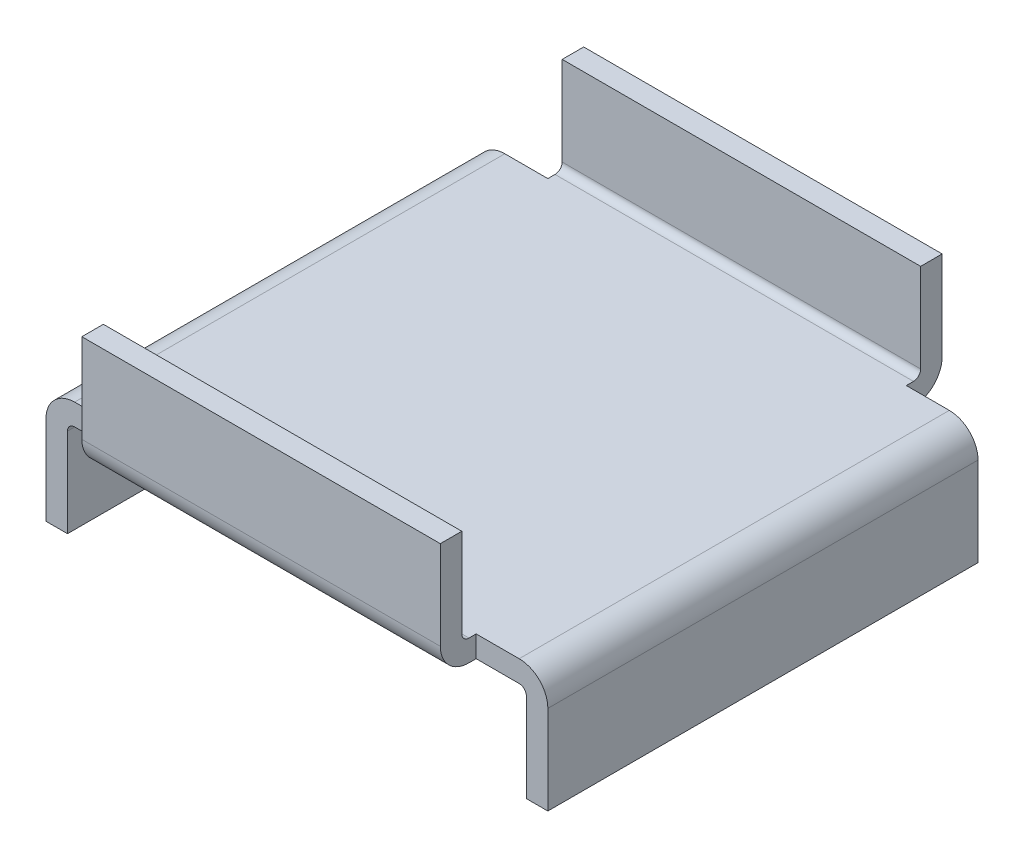
SolidWorks part; units mm, degrees
ref_plane "Front Plane" through (0, 0, 0) normal (0, 0, 1) x (1, 0, 0)
ref_plane "Top Plane" through (0, 0, 0) normal (0, 1, 0) x (1, 0, 0)
ref_plane "Right Plane" through (0, 0, 0) normal (1, 0, 0) x (0, 0, -1)
ref_plane "Plane1" through (0, 6.7, 0) normal (0, 1, 0) x (1, 0, 0)
sketch "Sketch1" plane through (0, 6.7, 0) normal (0, 1, 0) x (1, 0, 0)
  line L0 (12.5, -17.5) -> (12.5, 17.5)
  line L1 (12.5, 17.5) -> (-12.5, 17.5)
  line L2 (-12.5, 17.5) -> (-12.5, -17.5)
  line L3 (-12.5, -17.5) -> (12.5, -17.5)
  dimension "D1" = 25
extrude "Boss-Extrude1" add sketch "Sketch1" against normal blind 8.2
sketch "Sketch2" plane through (12.5, 0, 0) normal (1, 0, 0) x (0, 0, -1)
  line L0 (16, 6.7) -> (-16, 6.7)
  line L1 (-16, 6.7) -> (-16, 0)
  line L2 (-16, 0) -> (16, 0)
  line L3 (16, 0) -> (16, 6.7)
extrude "Cut-Extrude1" cut sketch "Sketch2" against normal through all
sketch "Sketch3" plane through (-12.5, 0, 0) normal (-1, 0, 0) x (0, 0, 1)
  line L0 (15, -1.5) -> (-15, -1.5)
  line L1 (-15, -1.5) -> (-15, 0)
  line L2 (-15, 0) -> (15, 0)
  line L3 (15, 0) -> (15, -1.5)
extrude "Boss-Extrude2" add sketch "Sketch3" along normal blind 5
sketch "Sketch4" plane through (0, -1.5, 0) normal (0, -1, 0) x (1, 0, 0)
  line L0 (-16, 15) -> (-16, -15)
  line L1 (-16, -15) -> (-17.5, -15)
  line L2 (-17.5, -15) -> (-17.5, 15)
  line L3 (-17.5, 15) -> (-16, 15)
  dimension "D1" = 30
extrude "Boss-Extrude3" add sketch "Sketch4" along normal blind 6.7
sketch "Sketch5" plane through (12.5, 0, 0) normal (1, 0, 0) x (0, 0, -1)
  line L0 (-15, -1.5) -> (-15, 0)
  line L1 (-15, 0) -> (15, 0)
  line L2 (15, 0) -> (15, -1.5)
  line L3 (15, -1.5) -> (-15, -1.5)
extrude "Boss-Extrude4" add sketch "Sketch5" along normal blind 5
sketch "Sketch6" plane through (0, -1.5, 0) normal (0, -1, 0) x (1, 0, 0)
  line L0 (16, 15) -> (17.5, 15)
  line L1 (17.5, 15) -> (17.5, -15)
  line L2 (17.5, -15) -> (16, -15)
  line L3 (16, -15) -> (16, 15)
extrude "Boss-Extrude5" add sketch "Sketch6" along normal blind 6.7
fillet "Fillet1" radius 0.5 4 edges at (16, -1.5, 0) (0, 0, 16) (0, 0, -16) (-16, -1.5, 0)
fillet "Fillet2" radius 2 4 edges at (0, -1.5, -17.5) (0, -1.5, 17.5) (-17.5, 0, 0) (17.5, 0, 0)
